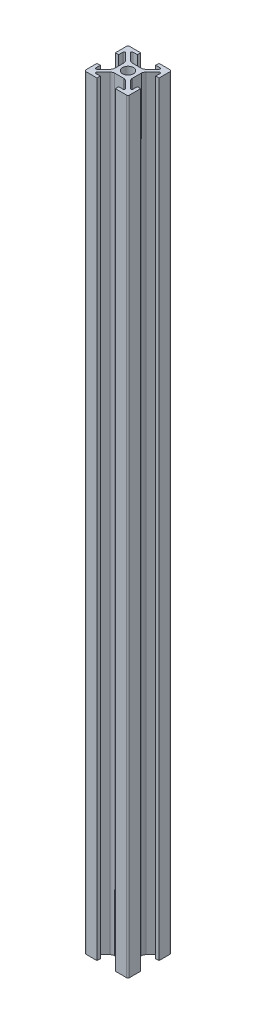
SolidWorks part; units mm, degrees
ref_plane "Front Plane" through (0, 0, 0) normal (0, 0, 1) x (1, 0, 0)
ref_plane "Top Plane" through (0, 0, 0) normal (0, 1, 0) x (1, 0, 0)
ref_plane "Right Plane" through (0, 0, 0) normal (1, 0, 0) x (0, 0, -1)
sketch "Sketch1" plane through (0, 0, 0) normal (0, 1, 0) x (1, 0, 0)
  line L0 (-3.611, 4.6716) -> (-6.5858, 7.6464)
  line L1 (9.25, -10) -> (4.2, -10)
  line L2 (10, -9.25) -> (10, -4.2)
  line L3 (9.25, 10) -> (4.2, 10)
  line L4 (-10, -9.25) -> (-10, -4.2)
  line L5 (10, -10) -> (-10, 10) construction
  line L6 (10, 10) -> (-10, -10) construction
  line L7 (2.2681, -4) -> (-2.2681, -4)
  line L8 (4, -2.2681) -> (4, 2.2681)
  line L9 (2.2681, 4) -> (-2.2681, 4)
  line L10 (-4, -2.2681) -> (-4, 2.2681)
  line L11 (4, -4) -> (-4, 4) construction
  line L12 (4, 4) -> (-4, -4) construction
  line L13 (-6.2322, 8.5) -> (-4.2, 8.5)
  line L14 (-4.2, 8.5) -> (-4.2, 10)
  line L15 (4.6716, 3.611) -> (7.6464, 6.5858)
  line L16 (8.5, 6.2322) -> (8.5, 4.2)
  line L17 (8.5, 4.2) -> (10, 4.2)
  line L18 (4.2, 8.5) -> (4.2, 10)
  line L19 (-8.5, 4.2) -> (-10, 4.2)
  line L20 (-8.5, 6.2322) -> (-8.5, 4.2)
  line L21 (-4.6716, 3.611) -> (-7.6464, 6.5858)
  line L22 (0, 10) -> (0, -10) construction
  line L23 (6.2322, 8.5) -> (4.2, 8.5)
  line L24 (3.611, 4.6716) -> (6.5858, 7.6464)
  line L25 (-55, 0) -> (55, 0) construction
  line L26 (3.611, -4.6716) -> (6.5858, -7.6464)
  line L27 (6.2322, -8.5) -> (4.2, -8.5)
  line L28 (-4.6716, -3.611) -> (-7.6464, -6.5858)
  line L29 (-8.5, -6.2322) -> (-8.5, -4.2)
  line L30 (-8.5, -4.2) -> (-10, -4.2)
  line L31 (4.2, -8.5) -> (4.2, -10)
  line L32 (8.5, -4.2) -> (10, -4.2)
  line L33 (8.5, -6.2322) -> (8.5, -4.2)
  line L34 (4.6716, -3.611) -> (7.6464, -6.5858)
  line L35 (-4.2, -8.5) -> (-4.2, -10)
  line L36 (-6.2322, -8.5) -> (-4.2, -8.5)
  line L37 (2.2681, -4) -> (-2.2681, -4)
  line L38 (10, -10) -> (4.2, -10)
  line L39 (-3.611, -4.6716) -> (-6.5858, -7.6464)
  line L40 (-4.2, 10) -> (-9.25, 10)
  line L41 (-10, 4.2) -> (-10, 9.25)
  line L42 (-4.2, -10) -> (-9.25, -10)
  line L43 (-4.2, -10) -> (-10, -10)
  line L44 (10, 4.2) -> (10, 9.25)
  circle A0 centre (0, 0) radius 2.5
  arc A1 (-8.5, 6.2322) -> (-7.6464, 6.5858) centre (-8, 6.2322) cw
  arc A2 (-6.5858, 7.6464) -> (-6.2322, 8.5) centre (-6.2322, 8) cw
  arc A3 (-3.611, 4.6716) -> (-2.2681, 4) centre (-1.7294, 6.7555) ccw
  arc A4 (-4.6716, 3.611) -> (-4, 2.2681) centre (-6.7555, 1.7294) cw
  arc A5 (4.6716, 3.611) -> (4, 2.2681) centre (6.7555, 1.7294) ccw
  arc A6 (3.611, 4.6716) -> (2.2681, 4) centre (1.7294, 6.7555) cw
  arc A7 (6.5858, 7.6464) -> (6.2322, 8.5) centre (6.2322, 8) ccw
  arc A8 (8.5, 6.2322) -> (7.6464, 6.5858) centre (8, 6.2322) ccw
  arc A9 (8.5, -6.2322) -> (7.6464, -6.5858) centre (8, -6.2322) cw
  arc A10 (6.5858, -7.6464) -> (6.2322, -8.5) centre (6.2322, -8) cw
  arc A11 (3.611, -4.6716) -> (2.2681, -4) centre (1.7294, -6.7555) ccw
  arc A12 (4.6716, -3.611) -> (4, -2.2681) centre (6.7555, -1.7294) cw
  arc A13 (-4.6716, -3.611) -> (-4, -2.2681) centre (-6.7555, -1.7294) ccw
  arc A14 (-3.611, -4.6716) -> (-2.2681, -4) centre (-1.7294, -6.7555) cw
  arc A15 (-6.5858, -7.6464) -> (-6.2322, -8.5) centre (-6.2322, -8) ccw
  arc A16 (-8.5, -6.2322) -> (-7.6464, -6.5858) centre (-8, -6.2322) ccw
  arc A17 (-9.25, -10) -> (-10, -9.25) centre (-9.25, -9.25) cw
  arc A18 (9.25, -10) -> (10, -9.25) centre (9.25, -9.25) ccw
  arc A19 (10, 9.25) -> (9.25, 10) centre (9.25, 9.25) ccw
  arc A20 (-9.25, 10) -> (-10, 9.25) centre (-9.25, 9.25) ccw
  point P0 (0, 0)
  point P18 (-8.5, 7.4393)
  point P24 (-7.4393, 8.5)
  point P31 (-2.2681, 4)
  point P32 (-3.611, 4.6716)
  point P50 (7.4393, 8.5)
  point P51 (8.5, 7.4393)
  point P86 (8.5, -7.4393)
  point P87 (7.4393, -8.5)
  point P88 (-7.4393, -8.5)
  point P89 (-8.5, -7.4393)
  dimension "D2" = 5
  dimension "D7" = 0.5
  dimension "D8" = 0.75
  dimension "D1" = 20
  dimension "D3" = 8
  dimension "D4" = 1.5
  dimension "D5" = 1.5
  dimension "D6" = 8.4
extrude "Boss-Extrude1" add sketch "Sketch1" along normal blind 350 contours L40 A20 L41 L19 L20 A1 L21 A4 L10 A13 L28 A16 L29 L30 L4 A17 L42 L35 L36 A15 L39 A14 L7 A11 L26 A10 L27 L31 L1 A18 L2 L32 L33 A9 L34 A12 L8 A5 L15 A8 L16 L17 L44 A19 L3 L18 L23 A7 L24 A6 L9
